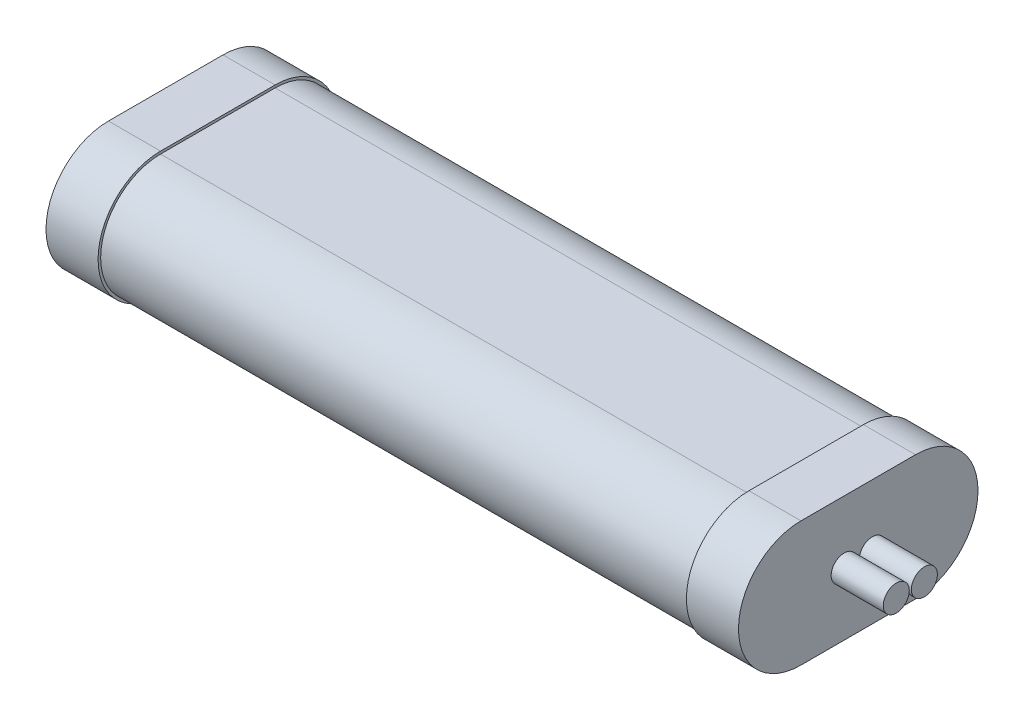
SolidWorks part; units mm, degrees
ref_plane "Front Plane" through (0, 0, 0) normal (0, 0, 1) x (1, 0, 0)
ref_plane "Top Plane" through (0, 0, 0) normal (0, 1, 0) x (1, 0, 0)
ref_plane "Right Plane" through (0, 0, 0) normal (1, 0, 0) x (0, 0, -1)
sketch "Sketch1" plane through (0, 0, 0) normal (1, 0, 0) x (0, 0, -1)
  line L0 (0, -51.2845) -> (0, 51.2845) construction
  line L1 (-79.1091, 0) -> (79.1091, 0) construction
  line L2 (-11, 11.5) -> (11, 11.5)
  line L3 (-11, -11.5) -> (11, -11.5)
  line L4 (22.5, -18.5251) -> (22.5, 18.5251) construction
  line L5 (-22.5, -18.5251) -> (-22.5, 18.5251) construction
  arc A0 (-11, 11.5) -> (-11, -11.5) centre (-11, 0) ccw
  arc A1 (11, 11.5) -> (11, -11.5) centre (11, 0) cw
  point P7 (0, 0)
  point P10 (0, 0)
  point P13 (0, 11.5)
  point P16 (0, -11.5)
  point P19 (22.5, 0)
  dimension "D1" = 23
  dimension "D2" = 45
  dimension "D3" = 11.5
extrude "Boss-Extrude1" add sketch "Sketch1" along normal mid plane 113
sketch "Sketch2" plane through (56.5, 0, 0) normal (1, 0, 0) x (0, 0, -1)
  line L0 (0, 0) -> (50000, 0) construction
  line L1 (0, 0) -> (0, 50000) construction
  line L2 (-11, 12) -> (11, 12)
  line L3 (-11, -12) -> (11, -12)
  line L4 (-23, -17.2291) -> (-23, 17.2291) construction
  line L6 (23, -17.2291) -> (23, 17.2291) construction
  arc A0 (-11, 12) -> (-11, -12) centre (-11, 0) ccw
  arc A1 (11, 12) -> (11, -12) centre (11, 0) cw
  point P8 (0, 12)
  point P15 (-23, 0)
  dimension "D2" = 46
  dimension "D1" = 24
extrude "Boss-Extrude2" add sketch "Sketch2" along normal blind 10
mirror "Mirror1" about plane through (0, 0, 0) normal (1, 0, 0) of "Boss-Extrude2"
sketch "Sketch3" plane through (66.5, 0, 0) normal (1, 0, 0) x (0, 0, -1)
  line L0 (0, 0) -> (50000, 0) construction
  line L1 (0, 0) -> (0, 50000) construction
  line L2 (-0.2, -4.7494) -> (-0.2, 4.7494) construction
  circle A0 centre (-2.7, 0) radius 2.5
  circle A1 centre (2.7, 0) radius 2.5
  point P10 (-0.2, 0)
  dimension "D2" = 5
  dimension "D1" = 0.2
extrude "Boss-Extrude3" add sketch "Sketch3" along normal blind 10
equation "\"D3@Sketch1\"=\"D1@Sketch1\" /2"
